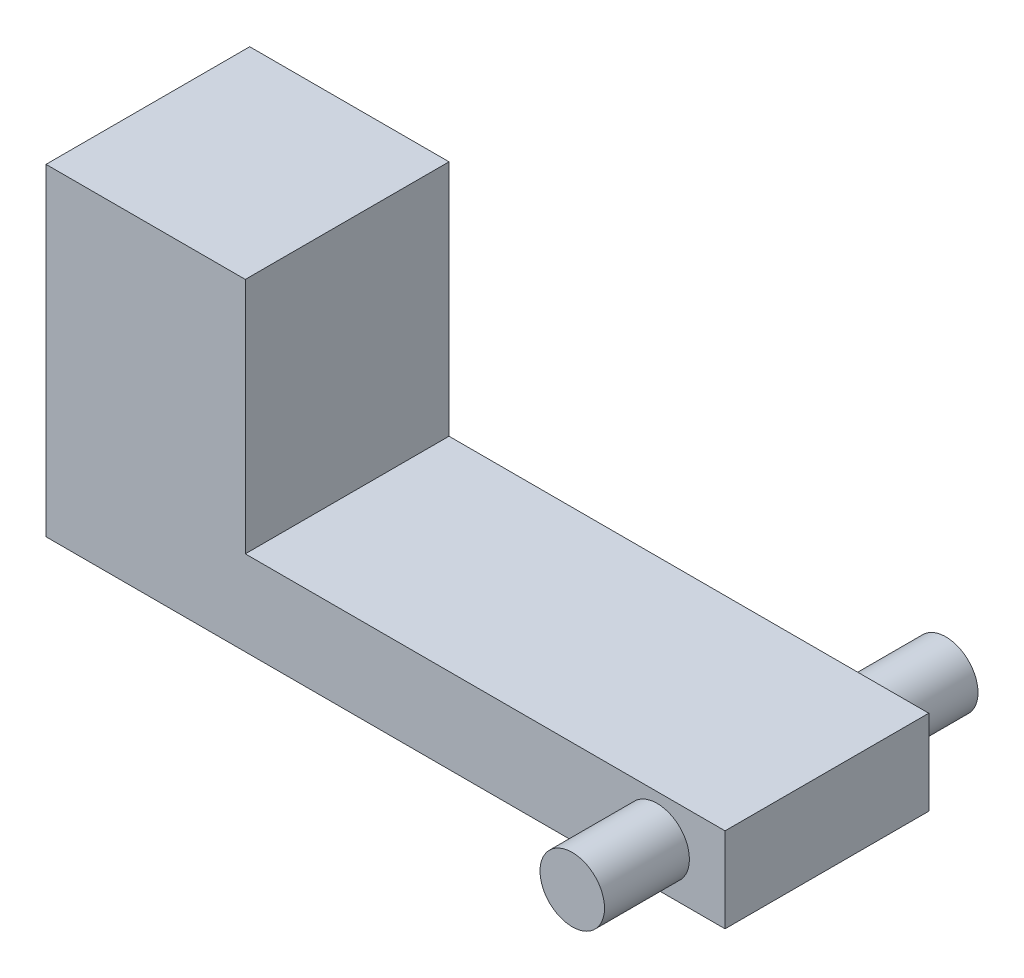
SolidWorks part; units mm, degrees
ref_plane "Front Plane" through (0, 0, 0) normal (0, 0, 1) x (1, 0, 0)
ref_plane "Top Plane" through (0, 0, 0) normal (0, 1, 0) x (1, 0, 0)
ref_plane "Right Plane" through (0, 0, 0) normal (1, 0, 0) x (0, 0, -1)
sketch "Sketch1" plane through (0, 0, 0) normal (0, 1, 0) x (1, 0, 0)
  line L1 (-10, -3) -> (10, -3)
  line L2 (-10, -3) -> (-10, 3)
  line L3 (-10, 3) -> (10, 3)
  line L4 (10, -3) -> (10, 3)
  line L5 (0, 3) -> (0, -3) construction
  line L6 (-10, 0) -> (10, 0) construction
  point P0 (0, 0)
  dimension "D1" = 20
  dimension "D2" = 6
extrude "Boss-Extrude1" add sketch "Sketch1" along normal blind 2.5
sketch "Sketch2" plane through (0, 0, 3) normal (0, 0, 1) x (1, 0, 0)
  line L0 (10, 2.5) -> (10, 0) construction
  line L1 (-10, 2.5) -> (10, 2.5) construction
  circle A0 centre (8, 1.25) radius 0.95
  dimension "D1" = 1.9
  dimension "D2" = 2
  dimension "D3" = 1.25
extrude "Boss-Extrude2" add sketch "Sketch2" along normal blind 2.5 and the other way blind 8.5
sketch "Sketch4" plane through (0, 2.5, 0) normal (0, 1, 0) x (1, 0, 0)
  line L0 (10, 3) -> (-10, 3) construction
  line L1 (-10, -3) -> (-4.1301, -3)
  line L2 (-10, -3) -> (-10, 3)
  line L3 (-10, 3) -> (-4.1301, 3)
  line L4 (-4.1301, -3) -> (-4.1301, 3)
extrude "Boss-Extrude3" add sketch "Sketch4" along normal blind 7
